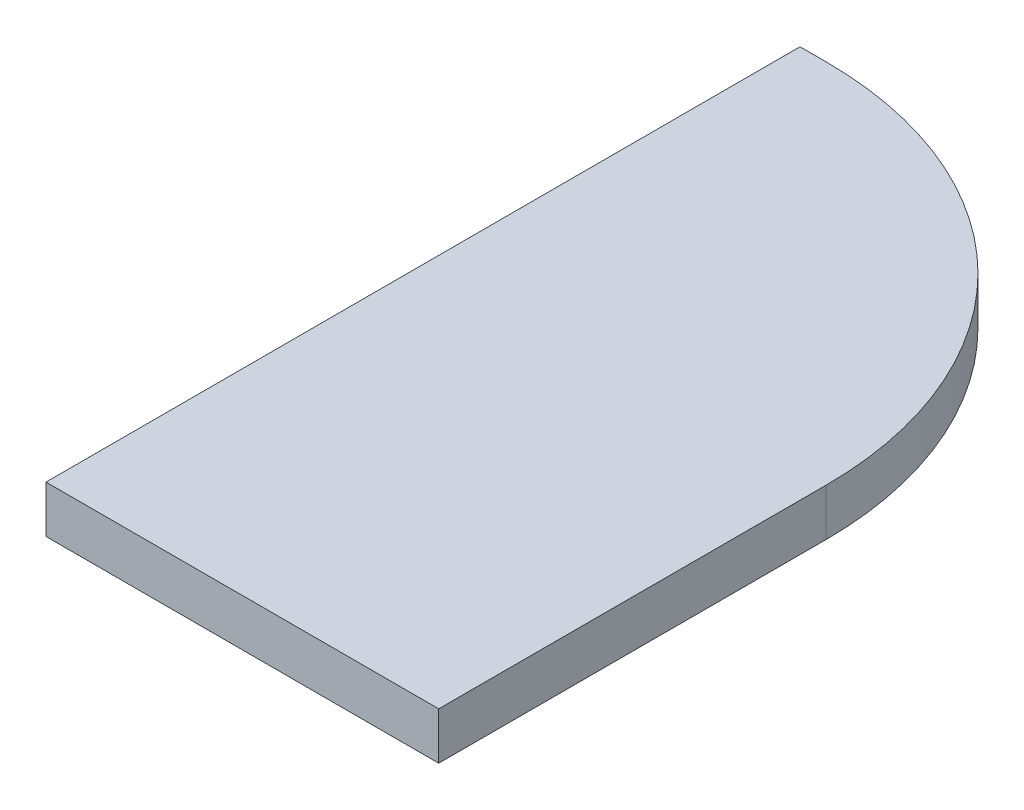
SolidWorks part; units mm, degrees
ref_plane "Front Plane" through (0, 0, 0) normal (0, 0, 1) x (1, 0, 0)
ref_plane "Top Plane" through (0, 0, 0) normal (0, 1, 0) x (1, 0, 0)
ref_plane "Right Plane" through (0, 0, 0) normal (1, 0, 0) x (0, 0, -1)
sketch "Sketch1" plane through (0, 0, 0) normal (0, 1, 0) x (1, 0, 0)
  line L1 (75, -144) -> (-75, -144)
  line L2 (75, -144) -> (75, 4)
  line L3 (-65, 144) -> (-75, 144)
  line L4 (-75, -144) -> (-75, 144)
  line L5 (75, -144) -> (-75, 144) construction
  line L6 (75, 144) -> (-75, -144) construction
  arc A0 (-65, 144) -> (75, 4) centre (-65, 4) cw
  point P0 (0, 0)
  dimension "D3" = 140
  dimension "D1" = 288
  dimension "D2" = 150
extrude "Boss-Extrude1" add sketch "Sketch1" along normal blind 18
equation "\"H_DSP\"=18"
equation "\"D1@Boss-Extrude1\"=\"H_DSP\""
